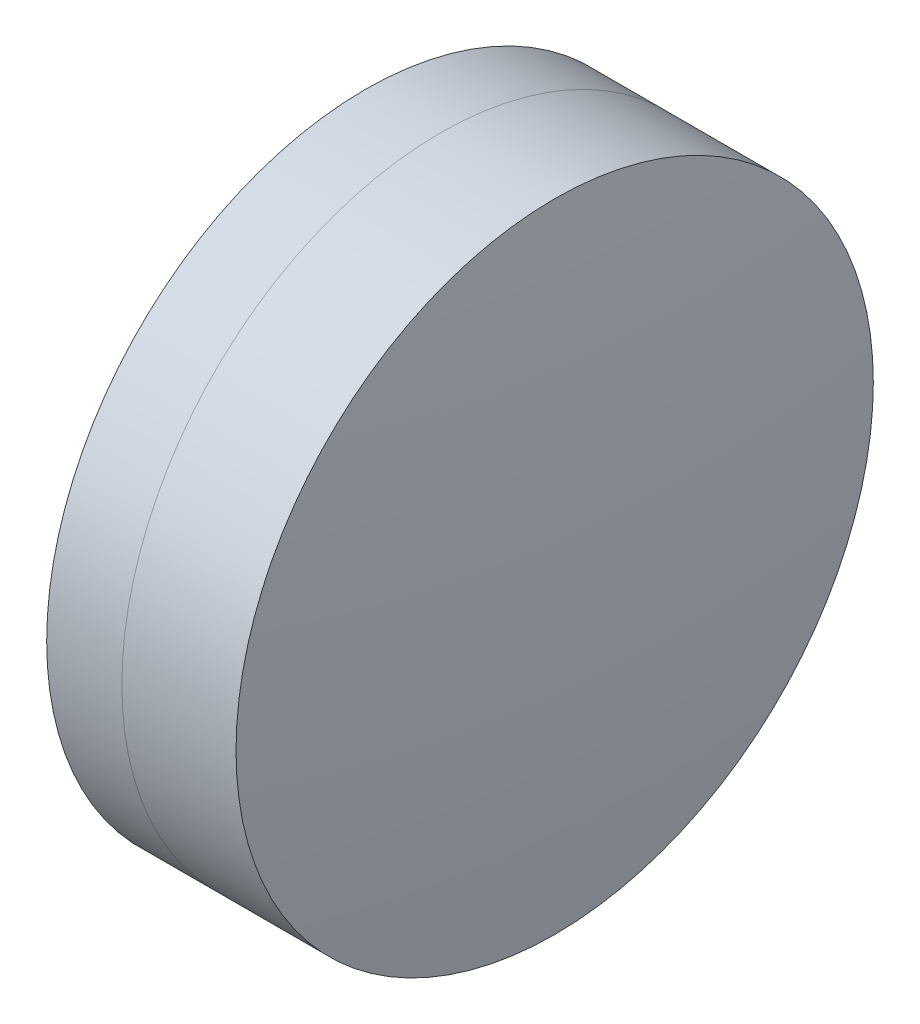
SolidWorks part; units mm, degrees
ref_plane "前视基准面" through (0, 0, 0) normal (0, 0, 1) x (1, 0, 0)
ref_plane "上视基准面" through (0, 0, 0) normal (0, 1, 0) x (1, 0, 0)
ref_plane "右视基准面" through (0, 0, 0) normal (1, 0, 0) x (0, 0, -1)
sketch "草图1" plane through (0, 0, 0) normal (0, 1, 0) x (1, 0, 0)
  line L0 (161.8332, 0) -> (266.0476, 0) construction
  line L1 (241.2493, -12.7) -> (244.2464, -12.7)
  line L2 (241.2493, 12.7) -> (244.2464, 12.7)
  arc A0 (244.2464, -12.7) -> (244.2464, 12.7) centre (211.0958, 0) ccw
  arc A1 (241.2493, 12.7) -> (241.2493, -12.7) centre (289.1958, 0) ccw
  point P10 (239.5958, 0)
  point P11 (246.5958, 0)
  dimension "D3" = 49.6
  dimension "D4" = 35.5
  dimension "D1" = 12.7
  dimension "D2" = 12.7
  dimension "D5" = 7
revolve "旋转1" add sketch "草图1" angle 360 about L0
sketch "草图2" plane through (0, 0, 0) normal (0, 1, 0) x (1, 0, 0)
  line L0 (-0.5519, 0) -> (253.9868, 0) construction
  line L2 (244.2464, 12.7) -> (248.7958, 12.7)
  line L3 (244.2464, -12.7) -> (248.7958, -12.7)
  arc A0 (248.7958, -12.7) -> (248.7958, 12.7) centre (148.3958, 0) ccw
  arc A1 (244.2464, -12.7) -> (244.2464, 12.7) centre (211.0958, 0) ccw construction
  arc A2 (244.2464, -12.7) -> (244.2464, 12.7) centre (211.0958, 0) ccw
  point P4 (246.5958, 0)
  point P8 (249.5958, 0)
  dimension "D1" = 101.2
  dimension "D2" = 3
revolve "旋转3" add sketch "草图2" angle 360 about L0
